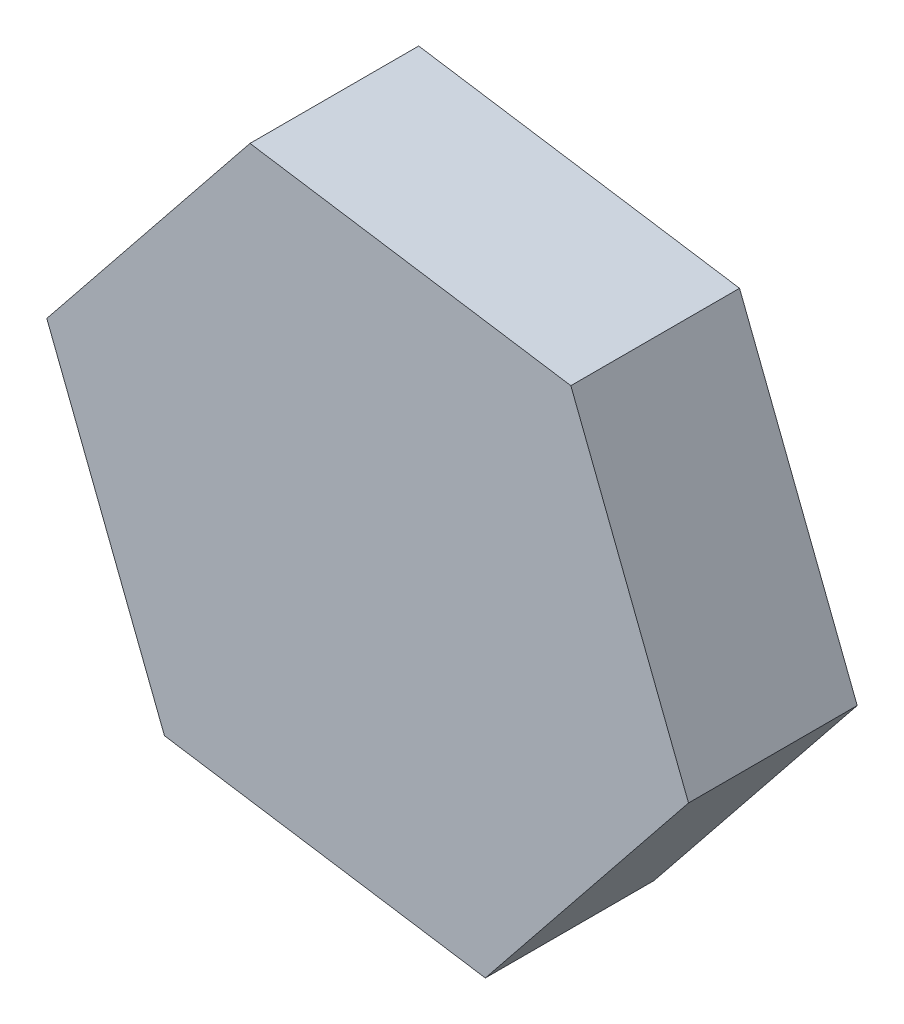
SolidWorks part; units mm, degrees
ref_plane "Alzado" through (0, 0, 0) normal (0, 0, 1) x (1, 0, 0)
ref_plane "Planta" through (0, 0, 0) normal (0, 1, 0) x (1, 0, 0)
ref_plane "Vista lateral" through (0, 0, 0) normal (1, 0, 0) x (0, 0, -1)
sketch "Croquis1" plane through (0, 0, 0) normal (0, 0, 1) x (1, 0, 0)
  line L1 (-54.3866, 4.2999) -> (-50.7729, 8.8026)
  line L2 (-50.7729, 8.8026) -> (-52.8655, 14.1835)
  line L3 (-52.8655, 14.1835) -> (-58.5718, 15.0617)
  line L4 (-58.5718, 15.0617) -> (-62.1855, 10.559)
  line L5 (-62.1855, 10.559) -> (-60.093, 5.1781)
  line L6 (-60.093, 5.1781) -> (-54.3866, 4.2999)
  circle A0 centre (-56.4792, 9.6808) radius 5 construction
  dimension "D1" = 5
extrude "Saliente-Extruir3" add sketch "Croquis1" along normal blind 3
sketch "Croquis3" plane through (0, 0, 0) normal (0, 0, 1) x (1, 0, 0)
  line L0 (-52.8655, 14.1835) -> (-58.5718, 15.0617) construction
  line L1 (-62.1855, 10.559) -> (-60.093, 5.1781) construction
  circle A0 centre (-56.4792, 9.6808) radius 2.5
  dimension "D1" = 5
  dimension "D2" = 5
